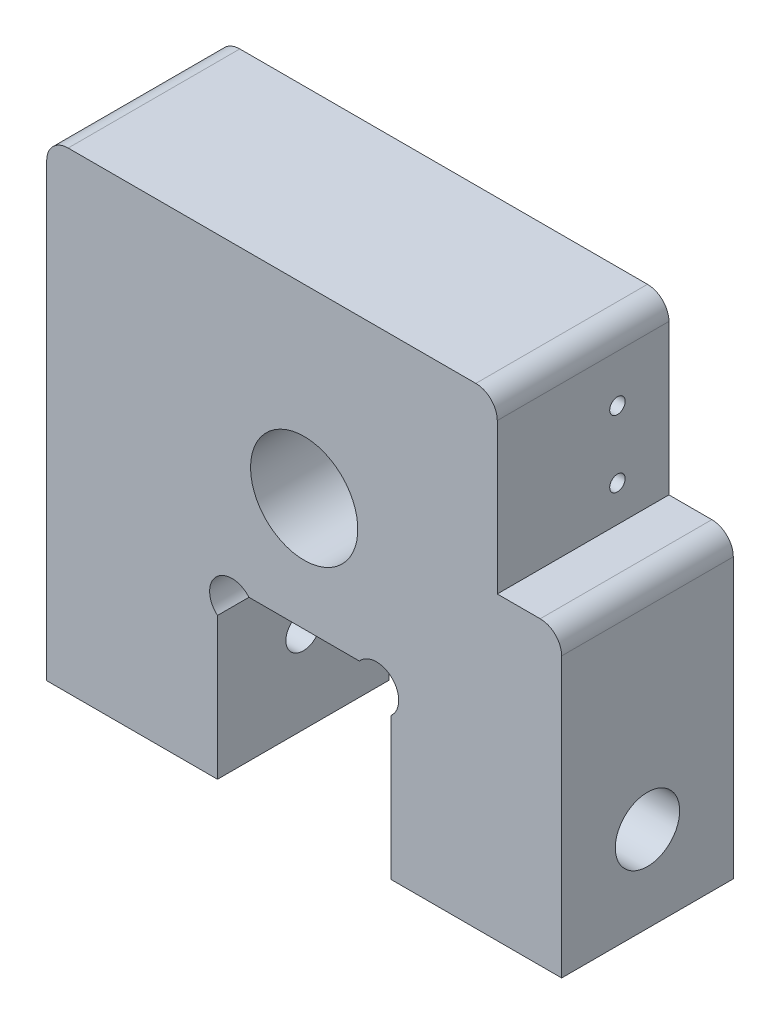
SolidWorks part; units mm, degrees
ref_plane "Front Plane" through (0, 0, 0) normal (0, 0, 1) x (1, 0, 0)
ref_plane "Top Plane" through (0, 0, 0) normal (0, 1, 0) x (1, 0, 0)
ref_plane "Right Plane" through (0, 0, 0) normal (1, 0, 0) x (0, 0, -1)
sketch "Sketch1" plane through (0, 0, 0) normal (0, 0, 1) x (1, 0, 0)
  line L0 (0, 0) -> (0, -22.098) construction
  line L1 (38.1, -34.925) -> (12.827, -34.925)
  line L2 (38.1, -34.925) -> (38.1, 9.525)
  line L3 (28.575, 34.925) -> (-38.1, 34.925)
  line L4 (-38.1, -34.925) -> (-38.1, 34.925)
  line L5 (38.1, -34.925) -> (-38.1, 34.925) construction
  line L6 (38.1, 34.925) -> (-38.1, -34.925) construction
  line L8 (12.827, -34.925) -> (12.827, -13.9255)
  line L9 (8.1725, -9.271) -> (-8.1725, -9.271)
  line L10 (-12.827, -34.925) -> (-12.827, -13.9255)
  line L11 (12.827, -34.925) -> (-12.827, -9.271) construction
  line L12 (12.827, -9.271) -> (-12.827, -34.925) construction
  line L14 (28.575, 9.525) -> (38.1, 9.525)
  line L15 (28.575, 9.525) -> (28.575, 30.099)
  line L18 (28.575, 9.525) -> (38.1, 30.099) construction
  line L19 (28.575, 30.099) -> (38.1, 9.525) construction
  line L20 (-12.827, -34.925) -> (-38.1, -34.925)
  line L21 (28.575, 30.099) -> (28.575, 34.925)
  arc A0 (-8.1725, -9.271) -> (-12.827, -13.9255) centre (-10.6882, -11.4098) ccw
  arc A1 (8.1725, -9.271) -> (12.827, -13.9255) centre (10.6882, -11.4098) cw
  circle A2 centre (0, 7.493) radius 6.35
  point P0 (0, 0)
  point P6 (0, -22.098)
  point P13 (33.3375, 19.812)
  dimension "D5" = 6.604
  dimension "D6" = 12.7
  dimension "D1" = 76.2
  dimension "D2" = 69.85
  dimension "D3" = 25.654
  dimension "D4" = 25.654
  dimension "D7" = 16.764
  dimension "D8" = 44.45
  dimension "D10" = 9.525
extrude "Boss-Extrude1" add sketch "Sketch1" along normal blind 25.4
sketch "Sketch2" plane through (0, 0, 0) normal (0, 0, -1) x (-1, 0, 0)
  circle A0 centre (0, 7.493) radius 7.9375
  dimension "D1" = 15.875
extrude "Cut-Extrude1" cut sketch "Sketch2" against normal through all
fillet "Fillet1" radius 3.175 3 edges at (-38.1, 34.925, 12.7) (38.1, 9.525, 12.7) (28.575, 34.925, 12.7)
sketch "Sketch3" plane through (38.1, 0, 0) normal (1, 0, 0) x (0, 0, -1)
  line L0 (-25.4, -34.925) -> (0, -34.925) construction
  circle A0 centre (-12.7, -22.225) radius 2.5797
  dimension "D1" = 5.1594
  dimension "D2" = 12.7
extrude "Cut-Extrude2" cut sketch "Sketch3" against normal up to vertex
sketch "Sketch4" plane through (-38.1, 0, 0) normal (-1, 0, 0) x (0, 0, 1)
  line L0 (0, 34.925) -> (25.4, 34.925) construction
  circle A0 centre (12.7, 28.575) radius 1.3525
  dimension "D2" = 2.7051
  dimension "D1" = 6.35
extrude "Cut-Extrude3" cut sketch "Sketch4" against normal blind 15.748
sketch "Sketch5" plane through (38.1, 0, 0) normal (1, 0, 0) x (0, 0, -1)
  circle A0 centre (-12.7, -22.225) radius 4.7625
  dimension "D1" = 9.525
extrude "Cut-Extrude4" cut sketch "Sketch5" against normal blind 10.3886
mirror "Mirror1" about plane through (0, 0, 0) normal (1, 0, 0) of "Cut-Extrude4"
sketch "Sketch6" plane through (28.575, 0, 0) normal (1, 0, 0) x (0, 0, -1)
  line L0 (-7.62, 14.859) -> (-7.62, 24.765) construction
  line L1 (0, 9.525) -> (0, 31.75) construction
  line L2 (-25.4, 9.525) -> (0, 9.525) construction
  circle A0 centre (-7.62, 14.859) radius 1.143
  circle A1 centre (-7.62, 24.765) radius 1.143
  dimension "D1" = 2.286
  dimension "D2" = 9.906
  dimension "D3" = 7.62
  dimension "D4" = 5.334
extrude "Cut-Extrude5" cut sketch "Sketch6" against normal blind 6.35
